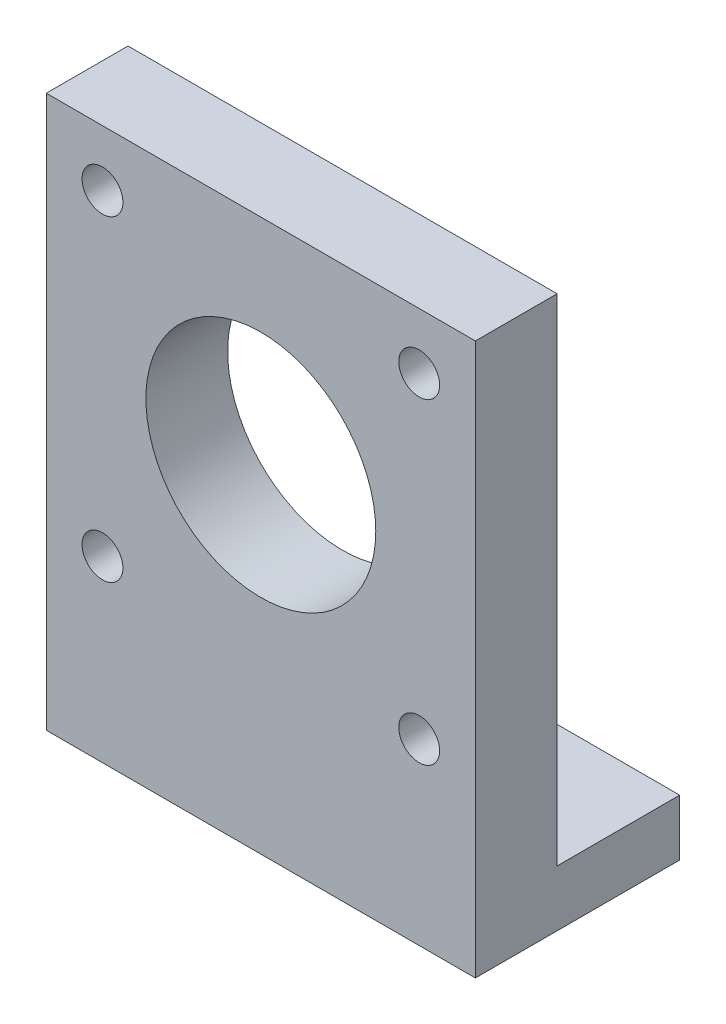
SolidWorks part; units mm, degrees
ref_plane "Plan de face" through (0, 0, 0) normal (0, 0, 1) x (1, 0, 0)
ref_plane "Plan de dessus" through (0, 0, 0) normal (0, 1, 0) x (1, 0, 0)
ref_plane "Plan de droite" through (0, 0, 0) normal (1, 0, 0) x (0, 0, -1)
sketch "Esquisse1" plane through (0, 0, 0) normal (0, 0, 1) x (1, 0, 0)
  line L1 (-21, 21) -> (21, 21)
  line L2 (-21, 21) -> (-21, -21)
  line L3 (-21, -21) -> (21, -21)
  line L4 (21, 21) -> (21, -21)
  line L5 (-21, 21) -> (21, -21) construction
  line L6 (-21, -21) -> (21, 21) construction
  line L7 (-15.5, 15.5) -> (15.5, 15.5) construction
  line L8 (-15.5, 15.5) -> (-15.5, -15.5) construction
  line L9 (-15.5, -15.5) -> (15.5, -15.5) construction
  line L10 (15.5, 15.5) -> (15.5, -15.5) construction
  line L11 (-15.5, 15.5) -> (15.5, -15.5) construction
  line L12 (-15.5, -15.5) -> (15.5, 15.5) construction
  circle A0 centre (-15.5, 15.5) radius 2
  circle A1 centre (15.5, 15.5) radius 2
  circle A2 centre (15.5, -15.5) radius 2
  circle A3 centre (-15.5, -15.5) radius 2
  circle A4 centre (0, 0) radius 11.25
  point P0 (0, 0)
  point P6 (0, 0)
  dimension "D2" = 4
  dimension "D4" = 22.5
  dimension "D1" = 42
  dimension "D3" = 31
  dimension "D5" = 42
extrude "Boss.-Extru.1" add sketch "Esquisse1" along normal blind 8
sketch "Esquisse2" plane through (0, 0, 8) normal (0, 0, 1) x (1, 0, 0)
  line L0 (-21, -21) -> (21, -21) construction
  line L1 (-21, -21) -> (21, -21)
  line L2 (-21, -21) -> (-21, -33)
  line L3 (-21, -33) -> (21, -33)
  line L4 (21, -21) -> (21, -33)
  line L5 (-21, -21) -> (21, -33) construction
  line L6 (-21, -33) -> (21, -21) construction
  line L7 (-21, 21) -> (-21, -21) construction
  line L8 (21, -21) -> (21, 21) construction
  point P0 (0, -27)
  dimension "D1" = 12
extrude "Boss.-Extru.2" add sketch "Esquisse2" against normal blind 8
sketch "Esquisse3" plane through (0, 0, 0) normal (0, 0, -1) x (-1, 0, 0)
  line L0 (21, 21) -> (21, -33) construction
  line L1 (-21, -27.5) -> (21, -27.5)
  line L2 (-21, -27.5) -> (-21, -33)
  line L3 (-21, -33) -> (21, -33)
  line L4 (21, -27.5) -> (21, -33)
  line L5 (-21, -27.5) -> (21, -33) construction
  line L6 (-21, -33) -> (21, -27.5) construction
  line L7 (-21, -33) -> (-21, 21) construction
  line L8 (21, -33) -> (-21, -33) construction
  point P0 (0, -30.25)
  dimension "D1" = 5.5
extrude "Boss.-Extru.3" add sketch "Esquisse3" along normal blind 12
